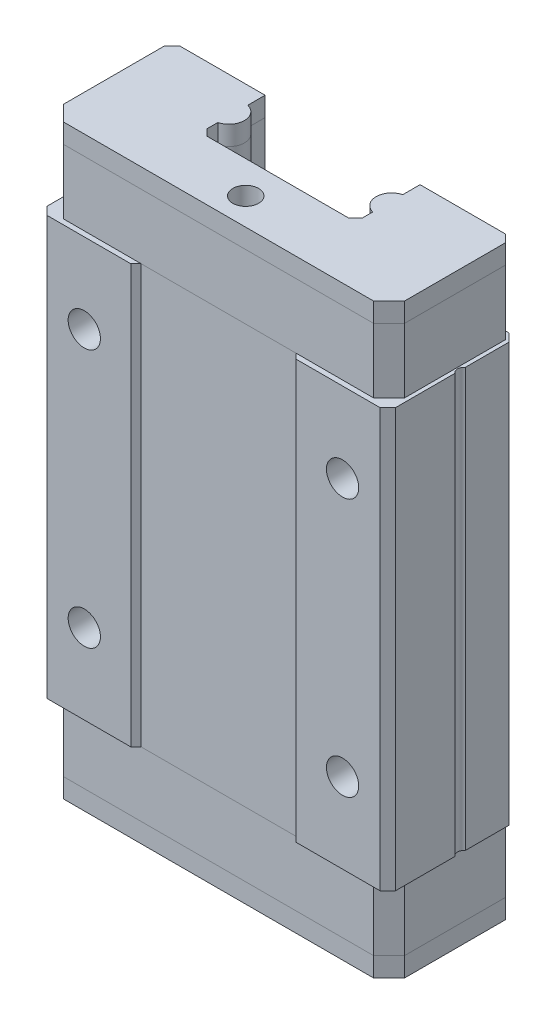
SolidWorks part; units mm, degrees
material "1.4301 (X5CrNi18-10)"
ref_plane "Horní rovina" through (0, 0, 0) normal (0, 0, 1) x (1, 0, 0)
ref_plane "Přední rovina" through (0, 0, 0) normal (0, 1, 0) x (1, 0, 0)
ref_plane "Pravá rovina" through (0, 0, 0) normal (1, 0, 0) x (0, 0, -1)
sketch "Skica1" plane through (0, 0, 0) normal (0, 0, 1) x (1, 0, 0)
  line L1 (-13.5, 16.2) -> (13.5, 16.2)
  line L2 (-13.5, 16.2) -> (-13.5, -16.2)
  line L3 (-13.5, -16.2) -> (13.5, -16.2)
  line L4 (13.5, 16.2) -> (13.5, -16.2)
  line L5 (-13.5, 16.2) -> (13.5, -16.2) construction
  line L6 (-13.5, -16.2) -> (13.5, 16.2) construction
  point P0 (0, 0)
  dimension "D1" = 27
  dimension "D2" = 32.4
extrude "Přidat vysunutím1" add sketch "Skica1" along normal blind 10
chamfer "Zkosení1" distance 0.6 angle 45 4 edges at (-13.5, 0, 0) (-13.5, 0, 10) (13.5, 0, 0) (13.5, 0, 10)
sketch "Skica2" plane through (0, -16.2, 0) normal (0, -1, 0) x (1, 0, 0)
  line L0 (0, 0) -> (0, 14.7686) construction
  line L1 (-12.9, 0) -> (12.9, 0) construction
  line L2 (-12.9, 10) -> (12.9, 10) construction
  line L4 (-6.4, 10) -> (6.4004, 10)
  line L5 (-6, 9.6) -> (6, 9.6)
  line L6 (-6.4, 10) -> (-6, 9.6)
  line L7 (6, 9.6) -> (6.4004, 10)
  point P9 (0.0002, 10)
  point P12 (0.0002, 10)
  point P15 (0, 9.6)
  dimension "D1" = 12
  dimension "D2" = 12.8004
  dimension "D3" = 0.4
extrude "Odebrat vysunutím1" cut sketch "Skica2" against normal through all
hole_wizard "M3 závit1" positions "Skica3" profile "Skica4" tap size "M3" standard "ISO"
sketch "Skica3" plane through (0, 0, 10) normal (0, 0, 1) x (1, 0, 0)
  line L1 (-8.5493, 0) -> (8.6735, 0) construction
  line L3 (0, 11.7876) -> (0, -10.7203) construction
  point P0 (-10, 10)
  point P2 (-10, -10)
  point P4 (10, -10)
  point P6 (10, 10)
  dimension "D1" = 10
  dimension "D2" = 10
  dimension "D3" = 10
  dimension "D4" = 10
  dimension "D5" = 10
  dimension "D6" = 10
  dimension "D7" = 10
  dimension "D8" = 10
sketch "Skica4" plane through (-10, 10, 10) normal (1, 0, 0) x (0, -1, 0)
  line L0 (0, 0) -> (0, 6.7511)
  line L1 (0, 6.7511) -> (1.25, 6)
  line L2 (1.25, 6) -> (1.25, 0)
  line L5 (1.25, 0) -> (0, 0)
  line L10 (0, 6.7511) -> (-1.25, 6) construction
  line L11 (0, -6.35) -> (0, 107.95) construction
  dimension "Průměr závitníku" = 2.5
  dimension "Hloubka závitníku" = 6
  dimension "Úhel vrtání" = 118
sketch "Skica5" plane through (0, -16.2, 0) normal (0, -1, 0) x (1, 0, 0)
  line L0 (-6, 9.6) -> (6, 9.6) construction
  line L1 (-6, 9.6) -> (6, 9.6)
  line L2 (0, -1.4037) -> (0, 13.1614) construction
  line L3 (6, 9.6) -> (12, 9.6)
  line L4 (13.2, 8.4) -> (13.2, 0.6)
  line L5 (13.5, 9.4) -> (13.5, 0.6) construction
  line L6 (12, 9.6) -> (13.2, 8.4)
  line L7 (13.2, 0.6) -> (12.6, 0)
  line L8 (-12.9, 0) -> (12.9, 0) construction
  line L9 (-12.6, 0) -> (12.6, 0)
  line L10 (-13.2, 0.6) -> (-12.6, 0)
  line L11 (-13.2, 8.4) -> (-13.2, 0.6)
  line L12 (-12, 9.6) -> (-13.2, 8.4)
  line L13 (-6, 9.6) -> (-12, 9.6)
  dimension "D1" = 0.3
  dimension "D2" = 1.2
  dimension "D3" = 1.2
  dimension "D4" = 45
  dimension "D5" = 0.6
extrude "Přidat vysunutím2" add sketch "Skica5" along normal blind 5 separate body
sketch "Skica6" plane through (0, -21.2, 0) normal (0, -1, 0) x (1, 0, 0)
  line L8 (12, 9.6) -> (-12, 9.6)
  line L9 (-12, 9.6) -> (-13.2, 8.4)
  line L10 (-13.2, 8.4) -> (-13.2, 0.6)
  line L11 (-13.2, 0.6) -> (-12.6, 0)
  line L12 (-12.6, 0) -> (12.6, 0)
  line L13 (12.6, 0) -> (13.2, 0.6)
  line L14 (13.2, 0.6) -> (13.2, 8.4)
  line L15 (13.2, 8.4) -> (12, 9.6)
  line L16 (12, 9.6) -> (-12, 9.6)
  line L17 (-12, 9.6) -> (-13.2, 8.4)
  line L18 (-13.2, 8.4) -> (-13.2, 0.6)
  line L19 (-13.2, 0.6) -> (-12.6, 0)
  line L20 (-12.6, 0) -> (12.6, 0)
  line L21 (12.6, 0) -> (13.2, 0.6)
  line L22 (13.2, 0.6) -> (13.2, 8.4)
  line L23 (13.2, 8.4) -> (12, 9.6)
  dimension "D1" = 0
extrude "Přidat vysunutím3" add sketch "Skica6" along normal blind 1.5
pattern_linear "LinPole1" count 2 spacing 37.4 along (0, 1, 0) of "Přidat vysunutím2"
pattern_linear "LinPole2" count 2 spacing 43.9 along (0, 1, 0) of "Přidat vysunutím3"
sketch "Skica7" plane through (0, -22.7, 0) normal (0, -1, 0) x (1, 0, 0)
  line L0 (-6, 1.3381) -> (-6, 0)
  line L1 (-6, 4.5) -> (-6, 3.6619)
  line L2 (-5.5, 5) -> (-6, 4.5)
  line L3 (-5.5, 5) -> (5.5, 5)
  line L4 (5.5, 5) -> (6, 4.5)
  line L5 (6, 4.5) -> (6, 3.6619)
  line L6 (6, 1.3381) -> (6, 0)
  line L7 (0, -0.8402) -> (0, 11.4147) construction
  line L8 (-12.6, 0) -> (12.6, 0) construction
  line L9 (-12.6, 0) -> (12.6, 0) construction
  line L10 (-6, 0) -> (6, 0)
  arc A0 (-6, 3.6619) -> (-6, 1.3381) centre (-6.3, 2.5) cw
  arc A2 (6, 3.6619) -> (6, 1.3381) centre (6.3, 2.5) ccw
  point P21 (0, 5)
  dimension "D5" = 1.2
  dimension "D1" = 5
  dimension "D2" = 6
  dimension "D3" = 0.5
  dimension "D4" = 0.5
  dimension "D6" = 2.5
  dimension "D7" = 6.3
extrude "Odebrat vysunutím2" cut sketch "Skica7" against normal through all
sketch "Skica8" plane through (0, -16.2, 0) normal (0, -1, 0) x (1, 0, 0)
  line L0 (13.5, 9.4) -> (13.5, 0.6) construction
  line L1 (6, 0) -> (12.9, 0) construction
  line L2 (13.5, 4.8) -> (13.5, 4)
  arc A0 (13.5, 4) -> (13.5, 4.8) centre (13.8, 4.4) cw
  dimension "D1" = 0.5
  dimension "D2" = 0.3
  dimension "D3" = 4.4
extrude "Odebrat vysunutím3" cut sketch "Skica8" against normal through all
sketch "Skica9" plane through (0, 22.7, 0) normal (0, 1, 0) x (1, 0, 0)
  line L0 (0, 0) -> (0, -11.8309) construction
  line L2 (12.9, -10) -> (6.4004, -10) construction
  circle A0 centre (0, -7.5) radius 1
  dimension "D1" = 2
  dimension "D2" = 2.5
extrude "Odebrat vysunutím4" cut sketch "Skica9" against normal blind 2
mirror "Zrcadlit4" about plane through (0, 0, 0) normal (0, 1, 0) of "Odebrat vysunutím4"
equation "\"D2@Skica3\" = \"D1@Skica3\""
equation "\"D3@Skica3\" = \"D1@Skica3\""
equation "\"D4@Skica3\" = \"D1@Skica3\""
equation "\"D5@Skica3\" = \"D1@Skica3\""
equation "\"D6@Skica3\" = \"D1@Skica3\""
equation "\"D7@Skica3\" = \"D1@Skica3\""
equation "\"D8@Skica3\" = \"D1@Skica3\""
equation "\"D3@Skica5\"=\"D2@Skica5\""
equation "\"D3@LinPole1\"= \"D2@Skica1\" + \"D1@Přidat vysunutím2\""
equation "\"D3@LinPole2\"= \"D2@Skica1\" + 2 * \"D1@Přidat vysunutím2\" + \"D1@Přidat vysunutím3\""
equation "\"D4@Skica7\"=\"D3@Skica7\""
